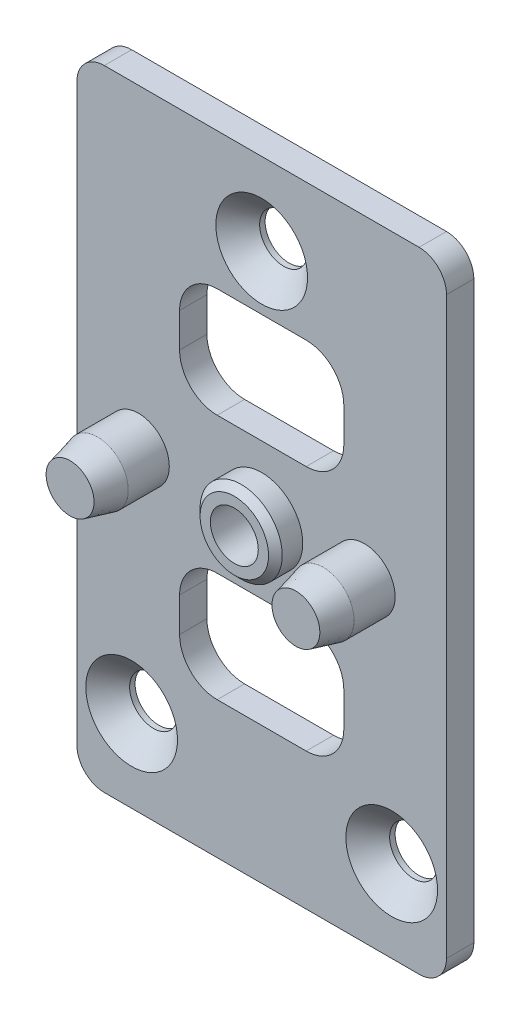
SolidWorks part; units mm, degrees
ref_plane "Front Plane" through (0, 0, 0) normal (0, 0, 1) x (1, 0, 0)
ref_plane "Top Plane" through (0, 0, 0) normal (0, 1, 0) x (1, 0, 0)
ref_plane "Right Plane" through (0, 0, 0) normal (1, 0, 0) x (0, 0, -1)
sketch "Sketch1" plane through (0, 0, 0) normal (0, 0, 1) x (1, 0, 0)
  line L0 (-13.5, 23) -> (13.5, -23) construction
  line L1 (-13.5, 23) -> (13.5, 23)
  line L2 (-13.5, 23) -> (-13.5, -23)
  line L3 (-13.5, -23) -> (13.5, -23)
  line L4 (13.5, 23) -> (13.5, -23)
  line L9 (0, 0) -> (0, 28.678) construction
  line L10 (0, 0) -> (-30.0335, 0) construction
  line L12 (-3.25, 13) -> (3.25, 13)
  line L13 (-6, 10.25) -> (-6, 7.75)
  line L14 (-3.25, 5) -> (3.25, 5)
  line L15 (6, 10.25) -> (6, 7.75)
  line L16 (-3.25, -5) -> (3.25, -5)
  line L17 (-6, -7.75) -> (-6, -10.25)
  line L18 (-3.25, -13) -> (3.25, -13)
  line L19 (6, -7.75) -> (6, -10.25)
  circle A0 centre (0, 0) radius 1.75
  circle A1 centre (0, 17) radius 1.75
  circle A3 centre (-9.5, -17) radius 1.75
  circle A4 centre (9.5, -17) radius 1.75
  arc A5 (-6, -10.25) -> (-3.25, -13) centre (-3.25, -10.25) ccw
  arc A6 (3.25, -13) -> (6, -10.25) centre (3.25, -10.25) ccw
  arc A7 (3.25, -5) -> (6, -7.75) centre (3.25, -7.75) cw
  arc A8 (-3.25, -5) -> (-6, -7.75) centre (-3.25, -7.75) ccw
  arc A9 (3.25, 13) -> (6, 10.25) centre (3.25, 10.25) cw
  arc A10 (3.25, 5) -> (6, 7.75) centre (3.25, 7.75) ccw
  arc A11 (-6, 7.75) -> (-3.25, 5) centre (-3.25, 7.75) ccw
  arc A12 (-3.25, 13) -> (-6, 10.25) centre (-3.25, 10.25) ccw
  point P2 (-13.5, -23)
  point P3 (13.5, 23)
  point P4 (0, 0)
  point P8 (0, 0)
  point P9 (0, 17)
  point P11 (0, -17)
  point P12 (0, -17)
  point P13 (0, -17)
  point P14 (0, 0)
  point P18 (0, 0)
  point P19 (0, 0)
  point P34 (0, 0)
  point P45 (6, 13)
  point P48 (6, 5)
  point P53 (-6, 13)
  point P54 (-7.0953, -17.9272)
  point P55 (0, 28.678)
  dimension "D3" = 3.5
  dimension "D4" = 17
  dimension "D12" = 2.75
  dimension "D7" = 3.5
  dimension "D1" = 27
  dimension "D2" = 46
  dimension "D6" = 17
  dimension "D5" = 19
  dimension "D10" = 12
  dimension "D11" = 8
  dimension "D13" = 10
  dimension "D14" = 10
extrude "Boss-Extrude1" add sketch "Sketch1" along normal mid plane 2
sketch "Sketch2" plane through (0, 0, 1) normal (0, 0, 1) x (1, 0, 0)
  circle A0 centre (0, 0) radius 3
  circle A1 centre (-9, 0) radius 2.25
  circle A2 centre (7.5, 0) radius 2.25
  circle A3 centre (0, 0) radius 1.75 construction
  circle A4 centre (0, 0) radius 1.75
  dimension "D1" = 9
  dimension "D3" = 4.5
  dimension "D4" = 6
  dimension "D2" = 7.5
extrude "Boss-Extrude2" add sketch "Sketch2" along normal blind 5
sketch "Sketch3" plane through (0, 0, 6) normal (0, 0, 1) x (1, 0, 0)
  circle A0 centre (0, 0) radius 3.5
  dimension "D1" = 7
extrude "Cut-Extrude1" cut sketch "Sketch3" against normal blind 3
chamfer "Chamfer1" distance 2 distance2 0.5 2 edges at (9.75, 0, 6) (-6.75, 0, 6)
chamfer "Chamfer2" distance 0.5 angle 45 1 edges at (3, 0, 3)
hole_wizard "CSK for M3 Flat Countersunk Head Screw1" positions "Sketch4" profile "Sketch5" countersink size "M3" standard "JIS" end condition up to next
sketch "Sketch4" plane through (0, 0, 1) normal (0, 0, 1) x (1, 0, 0)
  point P0 (0, 17)
  point P6 (-9.5, -17)
  point P9 (9.5, -17)
  point P12 (0, 0)
sketch "Sketch5" plane through (0, 17, 1) normal (1, 0, 0) x (0, -1, 0)
  line L0 (0, 0) -> (0, 2)
  line L1 (0, 2) -> (1.7, 2)
  line L2 (1.7, 2) -> (1.7, 1.65)
  line L3 (1.7, 1.65) -> (3.35, 0)
  line L5 (3.35, 0) -> (0, 0)
  line L6 (-1.7, 1.65) -> (-3.35, 0) construction
  line L11 (0, -6.35) -> (0, 107.95) construction
  dimension "Thru Hole Dia." = 3.4
  dimension "Thru Hole Depth" = 2
  dimension "Near C'Sink Dia." = 6.7
  dimension "Near C'Sink Angle" = 90
fillet "Fillet1" radius 2 4 edges at (13.5, -23, 0) (-13.5, -23, 0) (-13.5, 23, 0) (13.5, 23, 0)
